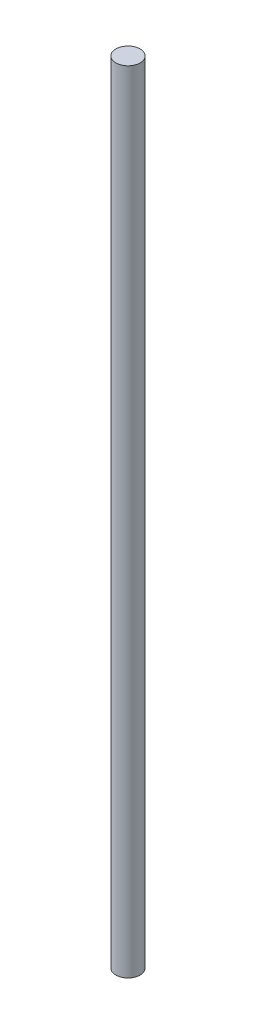
SolidWorks part; units mm, degrees
ref_plane "Front Plane" through (0, 0, 0) normal (0, 0, 1) x (1, 0, 0)
ref_plane "Top Plane" through (0, 0, 0) normal (0, 1, 0) x (1, 0, 0)
ref_plane "Right Plane" through (0, 0, 0) normal (1, 0, 0) x (0, 0, -1)
sketch "Sketch1" plane through (0, 0, 0) normal (0, 1, 0) x (1, 0, 0)
  circle A0 centre (0, 0) radius 914.4
  dimension "D1" = 1828.8
extrude "Boss-Extrude1" add sketch "Sketch1" along normal blind 59500.9784
